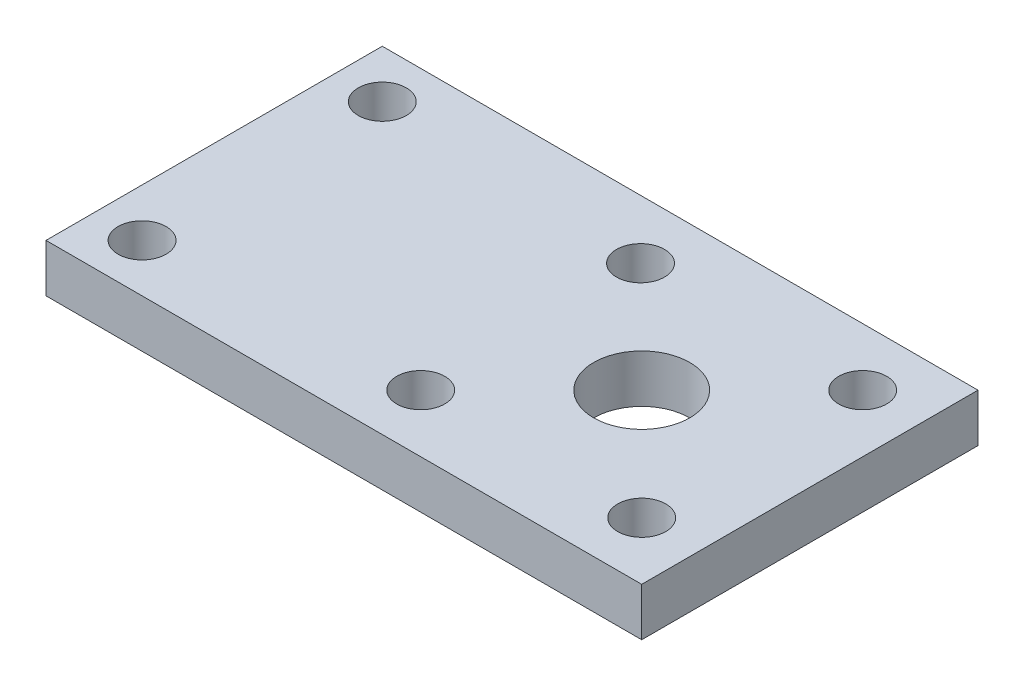
SolidWorks part; units mm, degrees
ref_plane "Front Plane" through (0, 0, 0) normal (0, 0, 1) x (1, 0, 0)
ref_plane "Top Plane" through (0, 0, 0) normal (0, 1, 0) x (1, 0, 0)
ref_plane "Right Plane" through (0, 0, 0) normal (1, 0, 0) x (0, 0, -1)
sketch "Sketch1" plane through (0, 0, 0) normal (0, 1, 0) x (1, 0, 0)
  line L1 (0, 0) -> (62, 0)
  line L2 (0, 0) -> (0, 35)
  line L3 (0, 35) -> (62, 35)
  line L4 (62, 0) -> (62, 35)
  dimension "D1" = 62
  dimension "D2" = 35
extrude "Boss-Extrude1" add sketch "Sketch1" along normal blind 5
sketch "Sketch2" plane through (0, 5, 0) normal (0, 1, 0) x (1, 0, 0)
  line L0 (0, 35) -> (0, 0) construction
  line L1 (62, 35) -> (0, 35) construction
  line L2 (0, 0) -> (62, 0) construction
  circle A0 centre (5, 30) radius 2.5
  circle A1 centre (5, 5) radius 2.5
  dimension "D1" = 5
  dimension "D2" = 5
  dimension "D3" = 5
  dimension "D4" = 5
  dimension "D5" = 5
extrude "Cut-Extrude1" cut sketch "Sketch2" against normal through all
sketch "Sketch3" plane through (0, 5, 0) normal (0, 1, 0) x (1, 0, 0)
  line L0 (62, 0) -> (62, 35) construction
  line L1 (62, 35) -> (0, 35) construction
  line L2 (0, 0) -> (62, 0) construction
  circle A0 centre (56, 29) radius 2.5
  circle A1 centre (56, 6) radius 2.5
  circle A2 centre (33, 28.8776) radius 2.5
  circle A3 centre (33, 6) radius 2.5
  circle A4 centre (44.5, 17.5) radius 5
  dimension "D1" = 5
  dimension "D7" = 10
  dimension "D2" = 6
  dimension "D3" = 6
  dimension "D4" = 6
  dimension "D5" = 6
  dimension "D6" = 23
  dimension "D8" = 17.5
  dimension "D9" = 17.5
extrude "Cut-Extrude2" cut sketch "Sketch3" against normal through all
